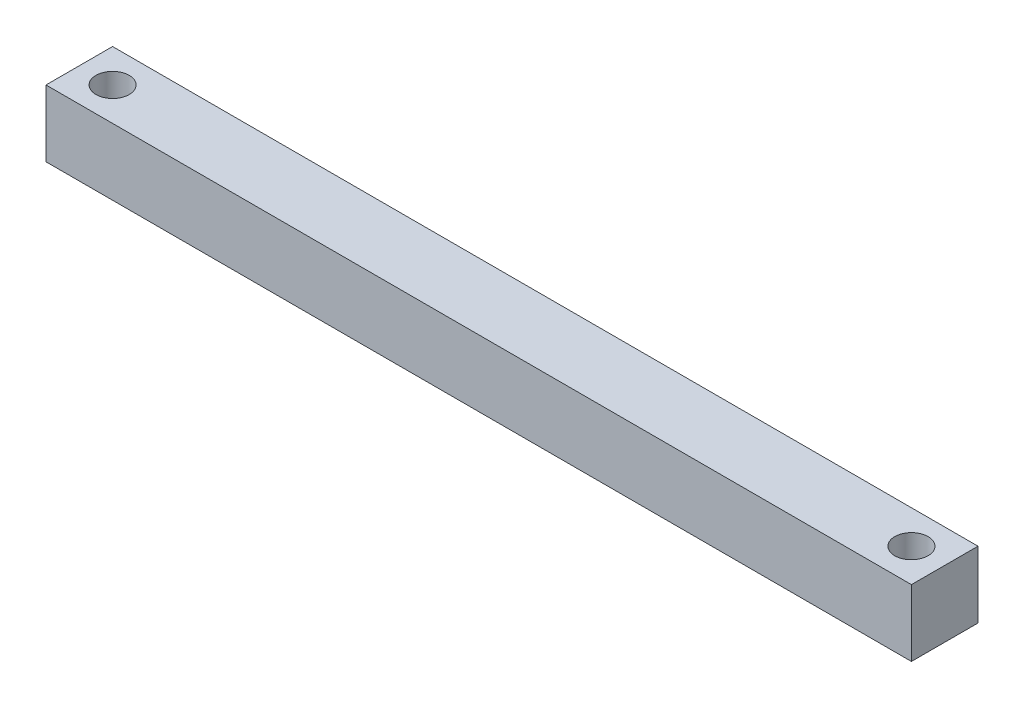
SolidWorks part; units mm, degrees
ref_plane "Front Plane" through (0, 0, 0) normal (0, 0, 1) x (1, 0, 0)
ref_plane "Top Plane" through (0, 0, 0) normal (0, 1, 0) x (1, 0, 0)
ref_plane "Right Plane" through (0, 0, 0) normal (1, 0, 0) x (0, 0, -1)
sketch "Sketch1" plane through (0, 0, 0) normal (1, 0, 0) x (0, 0, -1)
  line L1 (0, 0) -> (-25.4, 0)
  line L2 (0, 0) -> (0, 25.4)
  line L3 (0, 25.4) -> (-25.4, 25.4)
  line L4 (-25.4, 0) -> (-25.4, 25.4)
  dimension "D1" = 25.4
  dimension "D2" = 25.4
extrude "Boss-Extrude1" add sketch "Sketch1" along normal blind 330.2
sketch "Sketch2" plane through (0, 25.4, 0) normal (0, 1, 0) x (1, 0, 0)
  line L0 (330.2, 0) -> (0, 0) construction
  line L1 (330.2, 0) -> (330.2, -25.4) construction
  line L2 (0, 0) -> (0, -25.4) construction
  line L3 (330.2, -25.4) -> (0, -25.4) construction
  circle A0 centre (317.5, -12.7) radius 6.35
  circle A1 centre (12.7, -12.7) radius 6.35
  point P10 (0, -12.7)
  dimension "D1" = 12.7
  dimension "D2" = 12.7
  dimension "D3" = 12.7
  dimension "D4" = 12.7
  dimension "D5" = 12.7
  dimension "D6" = 12.7
extrude "Cut-Extrude1" cut sketch "Sketch2" against normal through all
